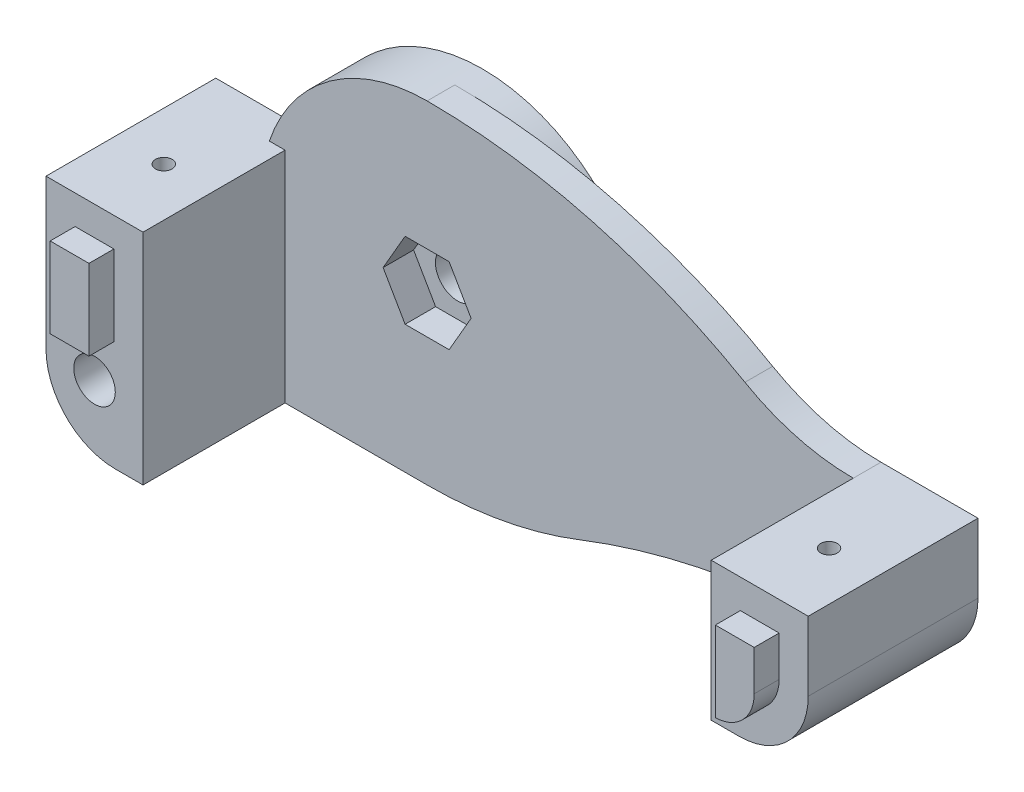
SolidWorks part; units mm, degrees
ref_plane "Alzado" through (0, 0, 0) normal (0, 0, 1) x (1, 0, 0)
ref_plane "Planta" through (0, 0, 0) normal (0, 1, 0) x (1, 0, 0)
ref_plane "Vista lateral" through (0, 0, 0) normal (1, 0, 0) x (0, 0, -1)
sketch "Croquis1" plane through (0, 0, 45.55) normal (0, 0, -1) x (-1, 0, 0)
  line L0 (-17.2407, 0.1428) -> (-17.2407, -9.8572) construction
  line L1 (13.5093, -15.6572) -> (25.5093, -15.6572) construction
  line L2 (25.5093, -15.6572) -> (25.5093, -3.6572) construction
  line L3 (-17.2407, 0.1428) -> (-17.2407, -9.8572)
  line L4 (13.5093, -15.6572) -> (25.5093, -15.6572)
  line L5 (25.5093, -15.6572) -> (25.5093, -3.6572)
  arc A0 (-17.2407, 0.1428) -> (-9.4241, 2.2272) centre (-17.2407, 15.8411) ccw construction
  arc A1 (2.5126, -13.5831) -> (-17.2407, -9.8572) centre (-17.2407, -64.0833) ccw construction
  arc A2 (2.5126, -13.5831) -> (13.5093, -15.6572) centre (13.5093, 14.5307) ccw construction
  arc A3 (25.5093, -3.6572) -> (13.5093, 8.3428) centre (13.5093, -3.6572) ccw construction
  arc A4 (13.5093, 8.3428) -> (-9.4241, 2.2272) centre (13.5093, -37.7151) ccw construction
  arc A5 (2.5126, -13.5831) -> (-17.2407, -9.8572) centre (-17.2407, -64.0833) ccw
  arc A6 (2.5126, -13.5831) -> (13.5093, -15.6572) centre (13.5093, 14.5307) ccw
  arc A7 (25.5093, -3.6572) -> (13.5093, 8.3428) centre (13.5093, -3.6572) ccw
  arc A8 (13.5093, 8.3428) -> (-9.4241, 2.2272) centre (13.5093, -37.7151) ccw
  arc A9 (-17.2407, 0.1428) -> (-9.4241, 2.2272) centre (-17.2407, 15.8411) ccw
extrude "Saliente-Extruir1" add sketch "Croquis1" along normal blind 2
sketch "Croquis2" plane through (17.2407, 0, 0) normal (1, 0, 0) x (0, 0, -1)
  line L1 (-43.55, 0.1428) -> (-55.8, 0.1428)
  line L2 (-43.55, 0.1428) -> (-43.55, -9.8572)
  line L3 (-43.55, -9.8572) -> (-55.8, -9.8572)
  line L4 (-55.8, 0.1428) -> (-55.8, -9.8572)
extrude "Saliente-Extruir2" add sketch "Croquis2" along normal up to surface (7 mm away)
fillet "Redondeo1" radius 5 1 edges at (24.2407, -9.8572, 49.675)
sketch "Croquis3" plane through (0, 0.1428, 0) normal (0, 1, 0) x (1, 0, 0)
  circle A0 centre (20.7407, -50.8) radius 0.6
  dimension "D1" = 1.2
extrude "Cortar-Extruir1" cut sketch "Croquis3" against normal blind 7.2
sketch "Croquis4" plane through (0, 0, 55.8) normal (0, 0, 1) x (1, 0, 0)
  line L19 (19.3407, -1.9572) -> (19.3407, -7.7555)
  line L20 (22.1407, -4.8572) -> (22.1407, -1.9572)
  line L21 (22.1407, -1.9572) -> (19.3407, -1.9572)
  line L22 (19.3407, -1.9572) -> (19.3407, -7.7555)
  line L23 (22.1407, -4.8572) -> (22.1407, -1.9572)
  line L24 (22.1407, -1.9572) -> (19.3407, -1.9572)
  arc A5 (19.3407, -7.7555) -> (22.1407, -4.8572) centre (19.2407, -4.8572) ccw
  arc A6 (19.3407, -7.7555) -> (22.1407, -4.8572) centre (19.2407, -4.8572) ccw
  dimension "D1" = 2.1
extrude "Saliente-Extruir3" add sketch "Croquis4" along normal blind 1.8
sketch "Croquis5" plane through (-23.7593, 0, 0) normal (-1, 0, 0) x (0, 0, 1)
  line L1 (55.8, 0.1428) -> (43.55, 0.1428)
  line L2 (55.8, 0.1428) -> (55.8, -15.6572)
  line L3 (55.8, -15.6572) -> (43.55, -15.6572)
  line L4 (43.55, 0.1428) -> (43.55, -15.6572)
extrude "Saliente-Extruir4" add sketch "Croquis5" along normal up to surface (7 mm away)
fillet "Redondeo2" radius 5 1 edges at (-30.7593, -15.6572, 49.675)
sketch "Croquis6" plane through (0, 0.1428, 0) normal (0, 1, 0) x (1, 0, 0)
  circle A0 centre (-27.2593, -50.8) radius 0.6
  dimension "D1" = 1.2
extrude "Cortar-Extruir2" cut sketch "Croquis6" against normal blind 9.8
sketch "Croquis7" plane through (0, 0, 55.8) normal (0, 0, 1) x (1, 0, 0)
  line L6 (-28.6593, -7.7572) -> (-25.8593, -7.7572)
  line L7 (-30.7593, 0.1428) -> (-23.7593, 0.1428) construction
  line L9 (-28.6593, -1.9572) -> (-28.6593, -10.6572)
  line L10 (-25.8593, -1.9572) -> (-28.6593, -1.9572)
  line L11 (-25.8593, -15.6572) -> (-25.8593, -1.9572)
  line L12 (-28.6593, -1.9572) -> (-28.6593, -7.7572)
  line L13 (-25.8593, -1.9572) -> (-28.6593, -1.9572)
  line L14 (-25.8593, -7.7572) -> (-25.8593, -1.9572)
  dimension "D2" = 7.9
  dimension "D1" = 2.1
extrude "Saliente-Extruir5" add sketch "Croquis7" along normal blind 1.8
sketch "Croquis8" plane through (0, 0, 55.8) normal (0, 0, 1) x (1, 0, 0)
  circle A0 centre (-27.2593, -10.8572) radius 1.5
  dimension "D1" = 3
extrude "Cortar-Extruir3" cut sketch "Croquis8" against normal blind 13.8
sketch "Croquis9" plane through (0, 0, 43.55) normal (0, 0, -1) x (-1, 0, 0)
  circle A0 centre (27.2593, -10.8572) radius 3
  dimension "D1" = 6
extrude "Cortar-Extruir4" cut sketch "Croquis9" against normal blind 6
sketch "Croquis10" plane through (0, 0, 43.55) normal (0, 0, -1) x (-1, 0, 0)
  circle A0 centre (13.5093, -3.6572) radius 12
extrude "Saliente-Extruir6" add sketch "Croquis10" along normal blind 2
sketch "Croquis11" plane through (0, 0, 45.55) normal (0, 0, 1) x (1, 0, 0)
  line L1 (-15.097, -0.9072) -> (-16.6847, -3.6572)
  line L2 (-16.6847, -3.6572) -> (-15.097, -6.4072)
  line L3 (-15.097, -6.4072) -> (-11.9216, -6.4072)
  line L4 (-11.9216, -6.4072) -> (-10.3339, -3.6572)
  line L5 (-10.3339, -3.6572) -> (-11.9216, -0.9072)
  line L6 (-11.9216, -0.9072) -> (-15.097, -0.9072)
  circle A0 centre (-13.5093, -3.6572) radius 2.75 construction
  dimension "D1" = 5.5
extrude "Cortar-Extruir5" cut sketch "Croquis11" against normal blind 2.2
sketch "Croquis12" plane through (0, 0, 45.55) normal (0, 0, 1) x (1, 0, 0)
  circle A0 centre (-13.5093, -3.6572) radius 1.6
  dimension "D1" = 3.2
extrude "Cortar-Extruir6" cut sketch "Croquis12" against normal blind 4.2
sketch "Croquis14" plane through (0, 0, 41.55) normal (0, 0, -1) x (-1, 0, 0)
  line L1 (13.5093, 0.9616) -> (9.5093, -1.3478)
  line L2 (9.5093, -1.3478) -> (9.5093, -5.9666)
  line L3 (9.5093, -5.9666) -> (13.5093, -8.276)
  line L4 (13.5093, -8.276) -> (17.5093, -5.9666)
  line L5 (17.5093, -5.9666) -> (17.5093, -1.3478)
  line L6 (17.5093, -1.3478) -> (13.5093, 0.9616)
  circle A0 centre (13.5093, -3.6572) radius 4 construction
  circle A1 centre (13.5093, -3.6572) radius 1.6
  dimension "D1" = 8
extrude "Saliente-Extruir7" add sketch "Croquis14" along normal blind 2
